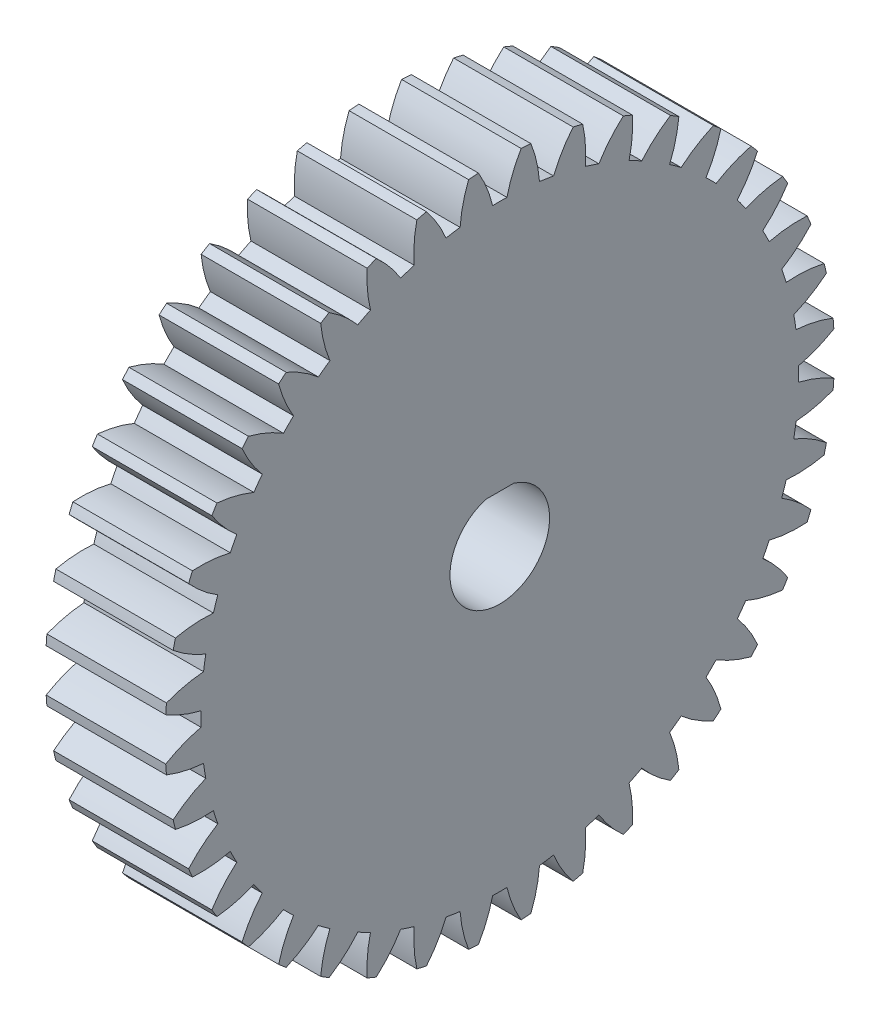
SolidWorks part; units mm, degrees
ref_plane "Front Plane" through (0, 0, 0) normal (0, 0, 1) x (1, 0, 0)
ref_plane "Top Plane" through (0, 0, 0) normal (0, 1, 0) x (1, 0, 0)
ref_plane "Right Plane" through (0, 0, 0) normal (1, 0, 0) x (0, 0, -1)
ref_plane "Plane4" through (6, 0, 0) normal (1, 0, 0) x (0, 0, -1)
sketch "Sketch1" plane through (6, 0, 0) normal (1, 0, 0) x (0, 0, -1)
  arc A0 (2.6995, 14.7541) -> (1.9919, 14.8662) centre (0, 0) ccw
  arc A1 (1.9919, 14.8662) -> (1.5645, 16.727) centre (-4.3896, 14.38) ccw
  arc A2 (1.5645, 16.727) -> (1.0715, 16.7658) centre (0, 0) ccw
  arc A3 (1.0715, 16.7658) -> (0.3582, 14.9947) centre (6.5851, 13.5163) ccw
  arc A4 (0.3582, 14.9947) -> (-0.3582, 14.9947) centre (0, 0) ccw
  arc A5 (-0.3582, 14.9947) -> (-1.0715, 16.7658) centre (-6.5851, 13.5163) ccw
  arc A6 (-1.0715, 16.7658) -> (-1.5645, 16.727) centre (0, 0) ccw
  arc A7 (-1.5645, 16.727) -> (-1.9919, 14.8662) centre (4.3896, 14.38) ccw
  arc A8 (-1.9919, 14.8662) -> (-2.6995, 14.7541) centre (0, 0) ccw
  arc A9 (-2.6995, 14.7541) -> (-3.681, 16.3918) centre (-8.6185, 12.3197) ccw
  arc A10 (-3.681, 16.3918) -> (-4.1619, 16.2763) centre (0, 0) ccw
  arc A11 (-4.1619, 16.2763) -> (-4.2929, 14.3715) centre (2.0861, 14.8897) ccw
  arc A12 (-4.2929, 14.3715) -> (-4.9743, 14.1501) centre (0, 0) ccw
  arc A13 (-4.9743, 14.1501) -> (-6.1999, 15.6141) centre (-10.4396, 10.8198) ccw
  arc A14 (-6.1999, 15.6141) -> (-6.6568, 15.4249) centre (0, 0) ccw
  arc A15 (-6.6568, 15.4249) -> (-6.4883, 13.523) centre (-0.2689, 15.0327) ccw
  arc A16 (-6.4883, 13.523) -> (-7.1267, 13.1978) centre (0, 0) ccw
  arc A17 (-7.1267, 13.1978) -> (-8.5662, 14.452) centre (-12.0037, 9.0535) ccw
  arc A18 (-8.5662, 14.452) -> (-8.9879, 14.1936) centre (0, 0) ccw
  arc A19 (-8.9879, 14.1936) -> (-8.5239, 12.3415) centre (-2.6172, 14.8055) ccw
  arc A20 (-8.5239, 12.3415) -> (-9.1035, 11.9204) centre (0, 0) ccw
  arc A21 (-9.1035, 11.9204) -> (-10.7215, 12.934) centre (-13.2721, 7.0643) ccw
  arc A22 (-10.7215, 12.934) -> (-11.0976, 12.6128) centre (0, 0) ccw
  arc A23 (-11.0976, 12.6128) -> (-10.3496, 10.8562) centre (-4.9011, 14.2138) ccw
  arc A24 (-10.3496, 10.8562) -> (-10.8562, 10.3496) centre (0, 0) ccw
  arc A25 (-10.8562, 10.3496) -> (-12.6128, 11.0976) centre (-14.2138, 4.9011) ccw
  arc A26 (-12.6128, 11.0976) -> (-12.934, 10.7215) centre (0, 0) ccw
  arc A27 (-12.934, 10.7215) -> (-11.9204, 9.1035) centre (-7.0643, 13.2721) ccw
  arc A28 (-11.9204, 9.1035) -> (-12.3415, 8.5239) centre (0, 0) ccw
  arc A29 (-12.3415, 8.5239) -> (-14.1936, 8.9879) centre (-14.8055, 2.6172) ccw
  arc A30 (-14.1936, 8.9879) -> (-14.452, 8.5662) centre (0, 0) ccw
  arc A31 (-14.452, 8.5662) -> (-13.1978, 7.1267) centre (-9.0535, 12.0037) ccw
  arc A32 (-13.1978, 7.1267) -> (-13.523, 6.4883) centre (0, 0) ccw
  arc A33 (-13.523, 6.4883) -> (-15.4249, 6.6568) centre (-15.0327, 0.2689) ccw
  arc A34 (-15.4249, 6.6568) -> (-15.6141, 6.1999) centre (0, 0) ccw
  arc A35 (-15.6141, 6.1999) -> (-14.1501, 4.9743) centre (-10.8198, 10.4396) ccw
  arc A36 (-14.1501, 4.9743) -> (-14.3715, 4.2929) centre (0, 0) ccw
  arc A37 (-14.3715, 4.2929) -> (-16.2763, 4.1619) centre (-14.8897, -2.0861) ccw
  arc A38 (-16.2763, 4.1619) -> (-16.3918, 3.681) centre (0, 0) ccw
  arc A39 (-16.3918, 3.681) -> (-14.7541, 2.6995) centre (-12.3197, 8.6185) ccw
  arc A40 (-14.7541, 2.6995) -> (-14.8662, 1.9919) centre (0, 0) ccw
  arc A41 (-14.8662, 1.9919) -> (-16.727, 1.5645) centre (-14.38, -4.3896) ccw
  arc A42 (-16.727, 1.5645) -> (-16.7658, 1.0715) centre (0, 0) ccw
  arc A43 (-16.7658, 1.0715) -> (-14.9947, 0.3582) centre (-13.5163, 6.5851) ccw
  arc A44 (-14.9947, 0.3582) -> (-14.9947, -0.3582) centre (0, 0) ccw
  arc A45 (-14.9947, -0.3582) -> (-16.7658, -1.0715) centre (-13.5163, -6.5851) ccw
  arc A46 (-16.7658, -1.0715) -> (-16.727, -1.5645) centre (0, 0) ccw
  arc A47 (-16.727, -1.5645) -> (-14.8662, -1.9919) centre (-14.38, 4.3896) ccw
  arc A48 (-14.8662, -1.9919) -> (-14.7541, -2.6995) centre (0, 0) ccw
  arc A49 (-14.7541, -2.6995) -> (-16.3918, -3.681) centre (-12.3197, -8.6185) ccw
  arc A50 (-16.3918, -3.681) -> (-16.2763, -4.1619) centre (0, 0) ccw
  arc A51 (-16.2763, -4.1619) -> (-14.3715, -4.2929) centre (-14.8897, 2.0861) ccw
  arc A52 (-14.3715, -4.2929) -> (-14.1501, -4.9743) centre (0, 0) ccw
  arc A53 (-14.1501, -4.9743) -> (-15.6141, -6.1999) centre (-10.8198, -10.4396) ccw
  arc A54 (-15.6141, -6.1999) -> (-15.4249, -6.6568) centre (0, 0) ccw
  arc A55 (-15.4249, -6.6568) -> (-13.523, -6.4883) centre (-15.0327, -0.2689) ccw
  arc A56 (-13.523, -6.4883) -> (-13.1978, -7.1267) centre (0, 0) ccw
  arc A57 (-13.1978, -7.1267) -> (-14.452, -8.5662) centre (-9.0535, -12.0037) ccw
  arc A58 (-14.452, -8.5662) -> (-14.1936, -8.9879) centre (0, 0) ccw
  arc A59 (-14.1936, -8.9879) -> (-12.3415, -8.5239) centre (-14.8055, -2.6172) ccw
  arc A60 (-12.3415, -8.5239) -> (-11.9204, -9.1035) centre (0, 0) ccw
  arc A61 (-11.9204, -9.1035) -> (-12.934, -10.7215) centre (-7.0643, -13.2721) ccw
  arc A62 (-12.934, -10.7215) -> (-12.6128, -11.0976) centre (0, 0) ccw
  arc A63 (-12.6128, -11.0976) -> (-10.8562, -10.3496) centre (-14.2138, -4.9011) ccw
  arc A64 (-10.8562, -10.3496) -> (-10.3496, -10.8562) centre (0, 0) ccw
  arc A65 (-10.3496, -10.8562) -> (-11.0976, -12.6128) centre (-4.9011, -14.2138) ccw
  arc A66 (-11.0976, -12.6128) -> (-10.7215, -12.934) centre (0, 0) ccw
  arc A67 (-10.7215, -12.934) -> (-9.1035, -11.9204) centre (-13.2721, -7.0643) ccw
  arc A68 (-9.1035, -11.9204) -> (-8.5239, -12.3415) centre (0, 0) ccw
  arc A69 (-8.5239, -12.3415) -> (-8.9879, -14.1936) centre (-2.6172, -14.8055) ccw
  arc A70 (-8.9879, -14.1936) -> (-8.5662, -14.452) centre (0, 0) ccw
  arc A71 (-8.5662, -14.452) -> (-7.1267, -13.1978) centre (-12.0037, -9.0535) ccw
  arc A72 (-7.1267, -13.1978) -> (-6.4883, -13.523) centre (0, 0) ccw
  arc A73 (-6.4883, -13.523) -> (-6.6568, -15.4249) centre (-0.2689, -15.0327) ccw
  arc A74 (-6.6568, -15.4249) -> (-6.1999, -15.6141) centre (0, 0) ccw
  arc A75 (-6.1999, -15.6141) -> (-4.9743, -14.1501) centre (-10.4396, -10.8198) ccw
  arc A76 (-4.9743, -14.1501) -> (-4.2929, -14.3715) centre (0, 0) ccw
  arc A77 (-4.2929, -14.3715) -> (-4.1619, -16.2763) centre (2.0861, -14.8897) ccw
  arc A78 (-4.1619, -16.2763) -> (-3.681, -16.3918) centre (0, 0) ccw
  arc A79 (-3.681, -16.3918) -> (-2.6995, -14.7541) centre (-8.6185, -12.3197) ccw
  arc A80 (-2.6995, -14.7541) -> (-1.9919, -14.8662) centre (0, 0) ccw
  arc A81 (-1.9919, -14.8662) -> (-1.5645, -16.727) centre (4.3896, -14.38) ccw
  arc A82 (-1.5645, -16.727) -> (-1.0715, -16.7658) centre (0, 0) ccw
  arc A83 (-1.0715, -16.7658) -> (-0.3582, -14.9947) centre (-6.5851, -13.5163) ccw
  arc A84 (-0.3582, -14.9947) -> (0.3582, -14.9947) centre (0, 0) ccw
  arc A85 (0.3582, -14.9947) -> (1.0715, -16.7658) centre (6.5851, -13.5163) ccw
  arc A86 (1.0715, -16.7658) -> (1.5645, -16.727) centre (0, 0) ccw
  arc A87 (1.5645, -16.727) -> (1.9919, -14.8662) centre (-4.3896, -14.38) ccw
  arc A88 (1.9919, -14.8662) -> (2.6995, -14.7541) centre (0, 0) ccw
  arc A89 (2.6995, -14.7541) -> (3.681, -16.3918) centre (8.6185, -12.3197) ccw
  arc A90 (3.681, -16.3918) -> (4.1619, -16.2763) centre (0, 0) ccw
  arc A91 (4.1619, -16.2763) -> (4.2929, -14.3715) centre (-2.0861, -14.8897) ccw
  arc A92 (4.2929, -14.3715) -> (4.9743, -14.1501) centre (0, 0) ccw
  arc A93 (4.9743, -14.1501) -> (6.1999, -15.6141) centre (10.4396, -10.8198) ccw
  arc A94 (6.1999, -15.6141) -> (6.6568, -15.4249) centre (0, 0) ccw
  arc A95 (6.6568, -15.4249) -> (6.4883, -13.523) centre (0.2689, -15.0327) ccw
  arc A96 (6.4883, -13.523) -> (7.1267, -13.1978) centre (0, 0) ccw
  arc A97 (7.1267, -13.1978) -> (8.5662, -14.452) centre (12.0037, -9.0535) ccw
  arc A98 (8.5662, -14.452) -> (8.9879, -14.1936) centre (0, 0) ccw
  arc A99 (8.9879, -14.1936) -> (8.5239, -12.3415) centre (2.6172, -14.8055) ccw
  arc A100 (8.5239, -12.3415) -> (9.1035, -11.9204) centre (0, 0) ccw
  arc A101 (9.1035, -11.9204) -> (10.7215, -12.934) centre (13.2721, -7.0643) ccw
  arc A102 (10.7215, -12.934) -> (11.0976, -12.6128) centre (0, 0) ccw
  arc A103 (11.0976, -12.6128) -> (10.3496, -10.8562) centre (4.9011, -14.2138) ccw
  arc A104 (10.3496, -10.8562) -> (10.8562, -10.3496) centre (0, 0) ccw
  arc A105 (10.8562, -10.3496) -> (12.6128, -11.0976) centre (14.2138, -4.9011) ccw
  arc A106 (12.6128, -11.0976) -> (12.934, -10.7215) centre (0, 0) ccw
  arc A107 (12.934, -10.7215) -> (11.9204, -9.1035) centre (7.0643, -13.2721) ccw
  arc A108 (11.9204, -9.1035) -> (12.3415, -8.5239) centre (0, 0) ccw
  arc A109 (12.3415, -8.5239) -> (14.1936, -8.9879) centre (14.8055, -2.6172) ccw
  arc A110 (14.1936, -8.9879) -> (14.452, -8.5662) centre (0, 0) ccw
  arc A111 (14.452, -8.5662) -> (13.1978, -7.1267) centre (9.0535, -12.0037) ccw
  arc A112 (13.1978, -7.1267) -> (13.523, -6.4883) centre (0, 0) ccw
  arc A113 (13.523, -6.4883) -> (15.4249, -6.6568) centre (15.0327, -0.2689) ccw
  arc A114 (15.4249, -6.6568) -> (15.6141, -6.1999) centre (0, 0) ccw
  arc A115 (15.6141, -6.1999) -> (14.1501, -4.9743) centre (10.8198, -10.4396) ccw
  arc A116 (14.1501, -4.9743) -> (14.3715, -4.2929) centre (0, 0) ccw
  arc A117 (14.3715, -4.2929) -> (16.2763, -4.1619) centre (14.8897, 2.0861) ccw
  arc A118 (16.2763, -4.1619) -> (16.3918, -3.681) centre (0, 0) ccw
  arc A119 (16.3918, -3.681) -> (14.7541, -2.6995) centre (12.3197, -8.6185) ccw
  arc A120 (14.7541, -2.6995) -> (14.8662, -1.9919) centre (0, 0) ccw
  arc A121 (14.8662, -1.9919) -> (16.727, -1.5645) centre (14.38, 4.3896) ccw
  arc A122 (16.727, -1.5645) -> (16.7658, -1.0715) centre (0, 0) ccw
  arc A123 (16.7658, -1.0715) -> (14.9947, -0.3582) centre (13.5163, -6.5851) ccw
  arc A124 (14.9947, -0.3582) -> (14.9947, 0.3582) centre (0, 0) ccw
  arc A125 (14.9947, 0.3582) -> (16.7658, 1.0715) centre (13.5163, 6.5851) ccw
  arc A126 (16.7658, 1.0715) -> (16.727, 1.5645) centre (0, 0) ccw
  arc A127 (16.727, 1.5645) -> (14.8662, 1.9919) centre (14.38, -4.3896) ccw
  arc A128 (14.8662, 1.9919) -> (14.7541, 2.6995) centre (0, 0) ccw
  arc A129 (14.7541, 2.6995) -> (16.3918, 3.681) centre (12.3197, 8.6185) ccw
  arc A130 (16.3918, 3.681) -> (16.2763, 4.1619) centre (0, 0) ccw
  arc A131 (16.2763, 4.1619) -> (14.3715, 4.2929) centre (14.8897, -2.0861) ccw
  arc A132 (14.3715, 4.2929) -> (14.1501, 4.9743) centre (0, 0) ccw
  arc A133 (14.1501, 4.9743) -> (15.6141, 6.1999) centre (10.8198, 10.4396) ccw
  arc A134 (15.6141, 6.1999) -> (15.4249, 6.6568) centre (0, 0) ccw
  arc A135 (15.4249, 6.6568) -> (13.523, 6.4883) centre (15.0327, 0.2689) ccw
  arc A136 (13.523, 6.4883) -> (13.1978, 7.1267) centre (0, 0) ccw
  arc A137 (13.1978, 7.1267) -> (14.452, 8.5662) centre (9.0535, 12.0037) ccw
  arc A138 (14.452, 8.5662) -> (14.1936, 8.9879) centre (0, 0) ccw
  arc A139 (14.1936, 8.9879) -> (12.3415, 8.5239) centre (14.8055, 2.6172) ccw
  arc A140 (12.3415, 8.5239) -> (11.9204, 9.1035) centre (0, 0) ccw
  arc A141 (11.9204, 9.1035) -> (12.934, 10.7215) centre (7.0643, 13.2721) ccw
  arc A142 (12.934, 10.7215) -> (12.6128, 11.0976) centre (0, 0) ccw
  arc A143 (12.6128, 11.0976) -> (10.8562, 10.3496) centre (14.2138, 4.9011) ccw
  arc A144 (10.8562, 10.3496) -> (10.3496, 10.8562) centre (0, 0) ccw
  arc A145 (10.3496, 10.8562) -> (11.0976, 12.6128) centre (4.9011, 14.2138) ccw
  arc A146 (11.0976, 12.6128) -> (10.7215, 12.934) centre (0, 0) ccw
  arc A147 (10.7215, 12.934) -> (9.1035, 11.9204) centre (13.2721, 7.0643) ccw
  arc A148 (9.1035, 11.9204) -> (8.5239, 12.3415) centre (0, 0) ccw
  arc A149 (8.5239, 12.3415) -> (8.9879, 14.1936) centre (2.6172, 14.8055) ccw
  arc A150 (8.9879, 14.1936) -> (8.5662, 14.452) centre (0, 0) ccw
  arc A151 (8.5662, 14.452) -> (7.1267, 13.1978) centre (12.0037, 9.0535) ccw
  arc A152 (7.1267, 13.1978) -> (6.4883, 13.523) centre (0, 0) ccw
  arc A153 (6.4883, 13.523) -> (6.6568, 15.4249) centre (0.2689, 15.0327) ccw
  arc A154 (6.6568, 15.4249) -> (6.1999, 15.6141) centre (0, 0) ccw
  arc A155 (6.1999, 15.6141) -> (4.9743, 14.1501) centre (10.4396, 10.8198) ccw
  arc A156 (4.9743, 14.1501) -> (4.2929, 14.3715) centre (0, 0) ccw
  arc A157 (4.2929, 14.3715) -> (4.1619, 16.2763) centre (-2.0861, 14.8897) ccw
  arc A158 (4.1619, 16.2763) -> (3.681, 16.3918) centre (0, 0) ccw
  arc A159 (3.681, 16.3918) -> (2.6995, 14.7541) centre (8.6185, 12.3197) ccw
  circle A160 centre (0, 0) radius 2.5
extrude "Boss-Extrude1" add sketch "Sketch1" against normal blind 6
sketch "Sketch2" plane through (6, 0, 0) normal (1, 0, 0) x (0, 0, -1)
  line L0 (-0.7, 2.4) -> (0.7, 2.4)
  arc A0 (0.7, 2.4) -> (-0.7, 2.4) centre (0, 0) ccw
  dimension "D2" = 5
  dimension "D1" = 2.4
extrude "Boss-Extrude2" add sketch "Sketch2" against normal blind 6
